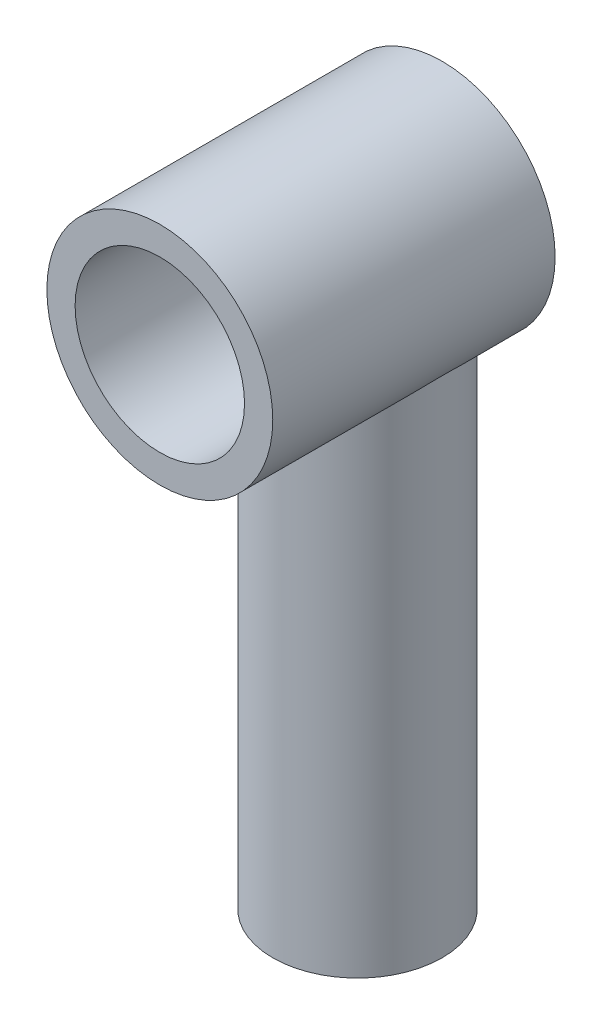
SolidWorks part; units mm, degrees
material "3.0255 (EN-AW 1350A)"
ref_plane "Plan de face" through (0, 0, 0) normal (0, 0, 1) x (1, 0, 0)
ref_plane "Plan de dessus" through (0, 0, 0) normal (0, 1, 0) x (1, 0, 0)
ref_plane "Plan de droite" through (0, 0, 0) normal (1, 0, 0) x (0, 0, -1)
sketch "Esquisse1" plane through (0, 0, 0) normal (0, 0, 1) x (1, 0, 0)
  circle A0 centre (0, 0) radius 4
  dimension "D1" = 8
extrude "Boss.-Extru.1" add sketch "Esquisse1" along normal blind 8 and the other way blind 2
sketch "Esquisse2" plane through (0, 0, 8) normal (0, 0, 1) x (1, 0, 0)
  circle A0 centre (0, 0) radius 3
  dimension "D1" = 6
sketch "Esquisse3" plane through (0, 0, 0) normal (0, 1, 0) x (1, 0, 0)
  line L0 (4, 2) -> (-4, 2) construction
  circle A0 centre (0, -1) radius 2
  circle A1 centre (0, -1) radius 3
  dimension "D1" = 6
  dimension "D2" = 4
sketch "Esquisse4" plane through (0, 0, 0) normal (0, 1, 0) x (1, 0, 0)
  circle A0 centre (0, -1) radius 2
  dimension "D1" = 4
extrude "Enlèv. mat.-Extru.2" cut sketch "Esquisse4" against normal blind 18
extrude "Boss.-Extru.2" add sketch "Esquisse3" along normal blind 1 and the other way blind 18 from offset 2.5 offset against normal yes
extrude "Enlèv. mat.-Extru.3" cut sketch "Esquisse2" against normal blind 9
